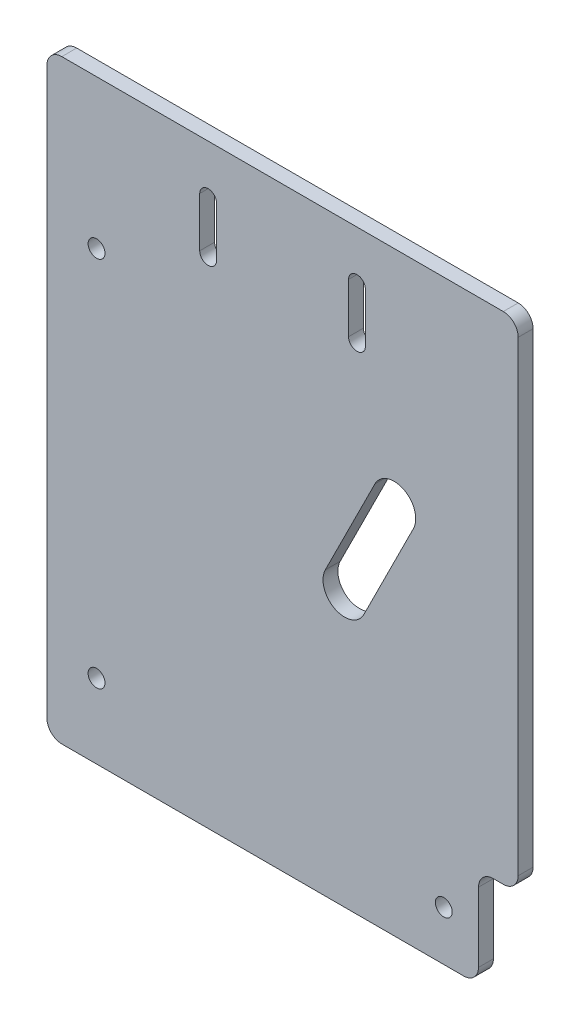
SolidWorks part; units mm, degrees
material "Acrylic (Medium-high impact)"
ref_plane "Front Plane" through (0, 0, 0) normal (0, 0, 1) x (1, 0, 0)
ref_plane "Top Plane" through (0, 0, 0) normal (0, 1, 0) x (1, 0, 0)
ref_plane "Right Plane" through (0, 0, 0) normal (1, 0, 0) x (0, 0, -1)
sketch "Sketch1" plane through (0, 0, 0) normal (0, 0, 1) x (1, 0, 0)
  line L0 (47.5, 0) -> (47.5, -120) construction
  line L1 (0, 0) -> (95, 0)
  line L2 (0, 0) -> (0, -120)
  line L3 (0, -120) -> (95, -120)
  line L4 (95, 0) -> (95, -120)
  line L5 (66.1092, -43.0546) -> (56.1092, -63.0546)
  line L6 (63.8908, -66.9454) -> (73.8908, -46.9454)
  circle A0 centre (60, -65) radius 4.35
  circle A1 centre (10, -30) radius 1.7
  circle A2 centre (10, -105) radius 1.7
  circle A3 centre (80, -110) radius 1.7
  circle A6 centre (70, -45) radius 4.35
  dimension "D4" = 8.7
  dimension "D8" = 3.4
  dimension "D9" = 3.4
  dimension "D11" = 8.7
  dimension "D14" = 3.4
  dimension "D1" = 120
  dimension "D2" = 95
  dimension "D3" = 60
  dimension "D5" = 55
  dimension "D6" = 15
  dimension "D7" = 75
  dimension "D10" = 10
  dimension "D12" = 10
  dimension "D13" = 20
  dimension "D15" = 10
  dimension "D16" = 15
extrude "Boss-Extrude1" add sketch "Sketch1" along normal blind 3
fillet "Fillet1" radius 3 4 edges at (95, -120, 1.5) (0, -120, 1.5) (95, 0, 1.5) (0, 0, 1.5)
sketch "Sketch2" plane through (0, 0, 3) normal (0, 0, 1) x (1, 0, 0)
  line L0 (3, 0) -> (92, 0) construction
  line L1 (32.5, -10) -> (62.5, -10) construction
  line L2 (47.5, 0) -> (47.5, -120) construction
  line L3 (3, -120) -> (92, -120) construction
  line L4 (30.8, -10) -> (30.8, -20)
  line L5 (34.2, -10) -> (34.2, -20)
  line L6 (60.8, -10) -> (60.8, -20)
  line L7 (64.2, -10) -> (64.2, -20)
  arc A0 (34.2, -10) -> (30.8, -10) centre (32.5, -10) ccw
  arc A1 (64.2, -10) -> (60.8, -10) centre (62.5, -10) ccw
  arc A2 (30.8, -20) -> (34.2, -20) centre (32.5, -20) ccw
  arc A3 (60.8, -20) -> (64.2, -20) centre (62.5, -20) ccw
  point P10 (47.5, -10)
  dimension "D3" = 3.4
  dimension "D4" = 3.4
  dimension "D1" = 30
  dimension "D2" = 110
  dimension "D5" = 10
extrude "Cut-Extrude1" cut sketch "Sketch2" against normal blind 10
sketch "Sketch3" plane through (0, 0, 3) normal (0, 0, 1) x (1, 0, 0)
  line L0 (95, -3) -> (95, -117) construction
  line L1 (95, -100) -> (87, -100)
  line L2 (95, -100) -> (95, -120)
  line L3 (95, -120) -> (87, -120)
  line L4 (87, -100) -> (87, -120)
  line L5 (3, -120) -> (92, -120) construction
  dimension "D1" = 8
  dimension "D2" = 20
extrude "Cut-Extrude2" cut sketch "Sketch3" against normal through all
fillet "Fillet2" radius 3 3 edges at (87, -120, 1.5) (87, -100, 1.5) (95, -100, 1.5)
equation "\"D11@Sketch1\"=\"D4@Sketch1\""
